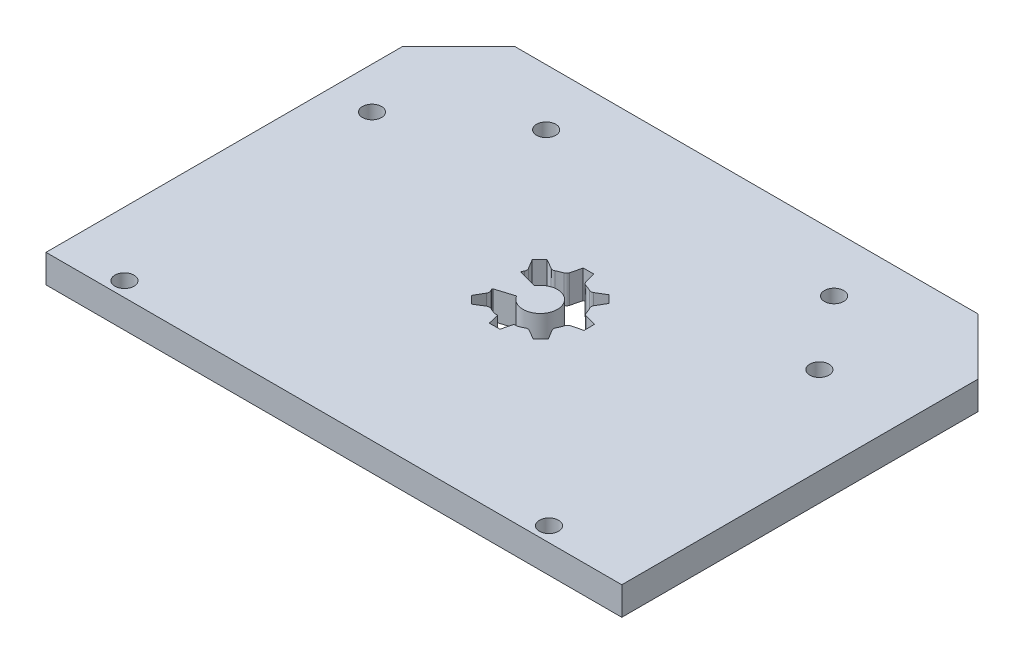
SolidWorks part; units mm, degrees
ref_plane "Alzado" through (0, 0, 0) normal (0, 0, 1) x (1, 0, 0)
ref_plane "Planta" through (0, 0, 0) normal (0, 1, 0) x (1, 0, 0)
ref_plane "Vista lateral" through (0, 0, 0) normal (1, 0, 0) x (0, 0, -1)
sketch "Croquis1" plane through (0, 0, 0) normal (0, 1, 0) x (1, 0, 0)
  line L0 (0, 53.1) -> (0, 63.1)
  line L1 (0, 0) -> (102, 0)
  line L2 (0, 0) -> (0, 53.1)
  line L4 (102, 0) -> (102, 53.1)
  line L5 (10, 73.1) -> (92, 73.1)
  line L6 (102, 63.1) -> (102, 53.1)
  line L7 (0, 63.1) -> (10, 73.1)
  line L8 (92, 73.1) -> (102, 63.1)
  line L11 (44.1881, 41.9347) -> (45.5015, 43.2703)
  line L12 (49.9908, 45.1742) -> (51.864, 45.19)
  line L13 (56.3847, 43.3619) -> (57.7203, 42.0485)
  line L14 (59.6242, 37.5592) -> (59.64, 35.686)
  line L15 (57.8119, 31.1653) -> (56.4985, 29.8297)
  line L16 (45.2096, 33.9979) -> (48.384, 34.9786)
  line L17 (44.1881, 41.9347) -> (45.2199, 40.2285)
  line L18 (52.0092, 28.4132) -> (50.136, 28.3975)
  line L19 (45.6153, 29.7381) -> (44.2797, 31.0515)
  line L20 (45.5015, 43.2703) -> (47.2249, 42.2674)
  line L21 (49.9908, 45.1742) -> (49.5139, 43.2382)
  line L22 (51.864, 45.19) -> (52.3734, 43.2622)
  line L23 (56.3847, 43.3619) -> (54.6785, 42.3301)
  line L24 (57.7203, 42.0485) -> (56.7174, 40.3251)
  line L25 (59.6242, 37.5592) -> (57.6882, 38.0361)
  line L26 (59.64, 35.686) -> (57.7122, 35.1766)
  line L27 (57.8119, 31.1653) -> (56.7801, 32.8715)
  line L28 (56.4985, 29.8297) -> (54.7751, 30.8326)
  line L29 (52.0092, 28.4132) -> (52.4861, 30.3493)
  line L30 (50.136, 28.3975) -> (49.6266, 30.3252)
  line L31 (45.6153, 29.7381) -> (47.3215, 30.7699)
  line L32 (44.2797, 31.0515) -> (45.2826, 32.7749)
  line L33 (48.4066, 38.1585) -> (45.1706, 39.0023)
  circle A0 centre (7.35, 50.4) radius 1.7
  circle A1 centre (11.3, 2.6) radius 1.7
  circle A2 centre (86.5, 50.5) radius 1.7
  circle A3 centre (86.5, 2.6) radius 1.7
  circle A4 centre (25.5, 63.1) radius 1.7
  circle A5 centre (76.5, 63.1) radius 1.7
  arc A6 (52.9667, 30.3756) -> (54.0717, 30.8443) centre (51, 36.55) ccw
  arc A7 (45.127, 33.8117) -> (45.2943, 33.4783) centre (51, 36.55) ccw
  arc A8 (45.2096, 33.9979) -> (45.127, 33.8117) centre (45.2495, 33.8688) ccw
  arc A9 (45.0813, 39.1881) -> (45.1706, 39.0023) centre (45.2047, 39.1331) ccw
  arc A10 (47.9283, 42.2557) -> (47.2249, 42.2674) centre (47.587, 42.8897) cw
  arc A11 (45.2434, 39.5253) -> (45.2199, 40.2285) centre (44.6038, 39.8559) ccw
  arc A12 (52.8625, 42.7566) -> (52.3734, 43.2622) centre (53.0695, 43.4462) cw
  arc A13 (49.0333, 42.7244) -> (49.5139, 43.2382) centre (48.8148, 43.4104) ccw
  arc A14 (56.7057, 39.6217) -> (56.7174, 40.3251) centre (57.3397, 39.963) cw
  arc A15 (53.9753, 42.3066) -> (54.6785, 42.3301) centre (54.3059, 42.9462) ccw
  arc A16 (57.2066, 34.6875) -> (57.7122, 35.1766) centre (57.8962, 34.4805) cw
  arc A17 (57.1744, 38.5167) -> (57.6882, 38.0361) centre (57.8604, 38.7352) ccw
  arc A18 (54.0717, 30.8443) -> (54.7751, 30.8326) centre (54.413, 30.2103) cw
  arc A19 (56.7566, 33.5747) -> (56.7801, 32.8715) centre (57.3962, 33.2441) ccw
  arc A20 (49.1375, 30.3434) -> (49.6266, 30.3252) centre (49.3568, 29.6577) cw
  arc A21 (52.9667, 30.3756) -> (52.4861, 30.3493) centre (52.7635, 29.6849) ccw
  arc A22 (45.2943, 33.4783) -> (45.2826, 32.7749) centre (44.6603, 33.137) cw
  arc A23 (48.0247, 30.7934) -> (47.3215, 30.7699) centre (47.6941, 30.1538) ccw
  arc A24 (48.0247, 30.7934) -> (49.1375, 30.3434) centre (51, 36.55) ccw
  arc A25 (45.2434, 39.5253) -> (45.0813, 39.1881) centre (51, 36.55) ccw
  arc A26 (49.0333, 42.7244) -> (47.9283, 42.2557) centre (51, 36.55) ccw
  arc A27 (53.9753, 42.3066) -> (52.8625, 42.7566) centre (51, 36.55) ccw
  arc A28 (57.1744, 38.5167) -> (56.7057, 39.6217) centre (51, 36.55) ccw
  arc A29 (56.7566, 33.5747) -> (57.2066, 34.6875) centre (51, 36.55) ccw
  arc A30 (48.384, 34.9786) -> (48.4066, 38.1585) centre (51, 36.55) ccw
  point P14 (0, 73.1)
  point P15 (102, 73.1)
  dimension "D3" = 3.4
  dimension "D8" = 3.4
  dimension "D9" = 3.4
  dimension "D14" = 3.4
  dimension "D16" = 3.4
  dimension "D17" = 3.4
  dimension "D1" = 102
  dimension "D2" = 53.1
  dimension "D4" = 7.35
  dimension "D6" = 11.3
  dimension "D7" = 2.6
  dimension "D10" = 2.6
  dimension "D11" = 15.5
  dimension "D12" = 15.5
  dimension "D15" = 20
extrude "Saliente-Extruir1" add sketch "Croquis1" along normal blind 5
